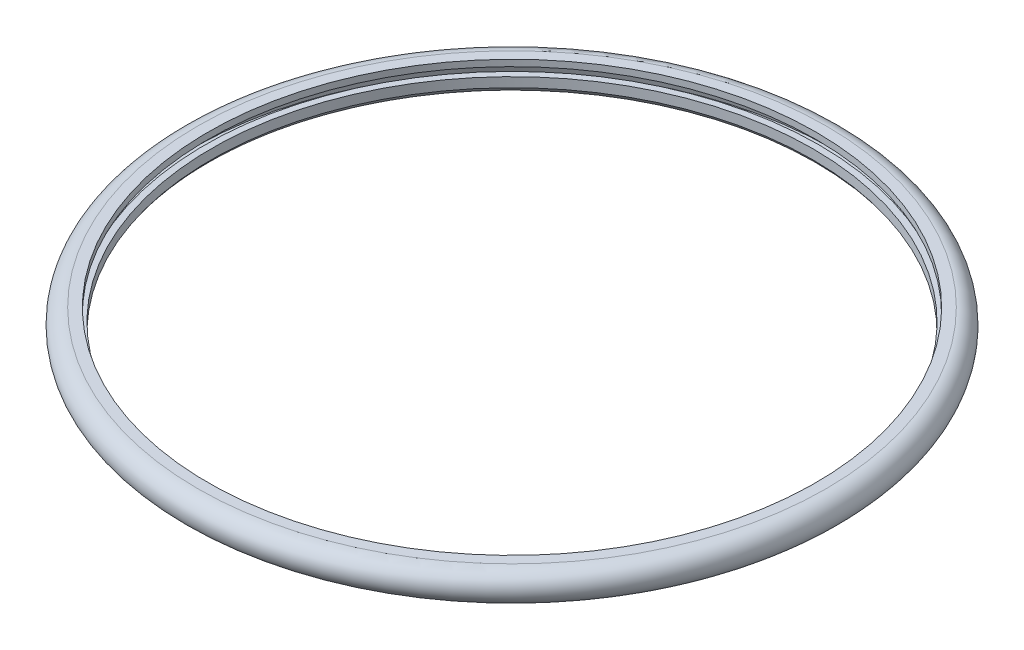
SolidWorks part; units mm, degrees
material "Rubber"
ref_plane "Front Plane" through (0, 0, 0) normal (0, 0, 1) x (1, 0, 0)
ref_plane "Top Plane" through (0, 0, 0) normal (0, 1, 0) x (1, 0, 0)
ref_plane "Right Plane" through (0, 0, 0) normal (1, 0, 0) x (0, 0, -1)
sketch "Sketch1" plane through (0, 0, 0) normal (0, 0, 1) x (1, 0, 0)
  line L17 (-24.6875, 1.25) -> (-25, 0)
  line L18 (-24.5625, 1.75) -> (-23.75, 1.75)
  line L20 (-24.6875, 1.25) -> (-23.75, 1.25)
  line L21 (-23.75, 1.75) -> (-23.75, 1.25)
  line L22 (-25, 0) -> (-24, 0)
  line L24 (-24, 0.75) -> (-23.5, 0.75)
  line L25 (-24, 0.75) -> (-24, 0)
  line L27 (-23.5, 0.75) -> (-23.5, 0)
  arc A0 (-24.5625, 1.75) -> (-23.5, 0) centre (-24.5625, 0.5525) ccw
  point P21 (-23.75, 0)
sketch "Sketch2" plane through (0, 0, 0) normal (0, 0, 1) x (1, 0, 0)
  line L0 (0, 0) -> (0, 5.8825) construction
revolve "Revolve1" add sketch "Sketch1" angle 360 about L0
